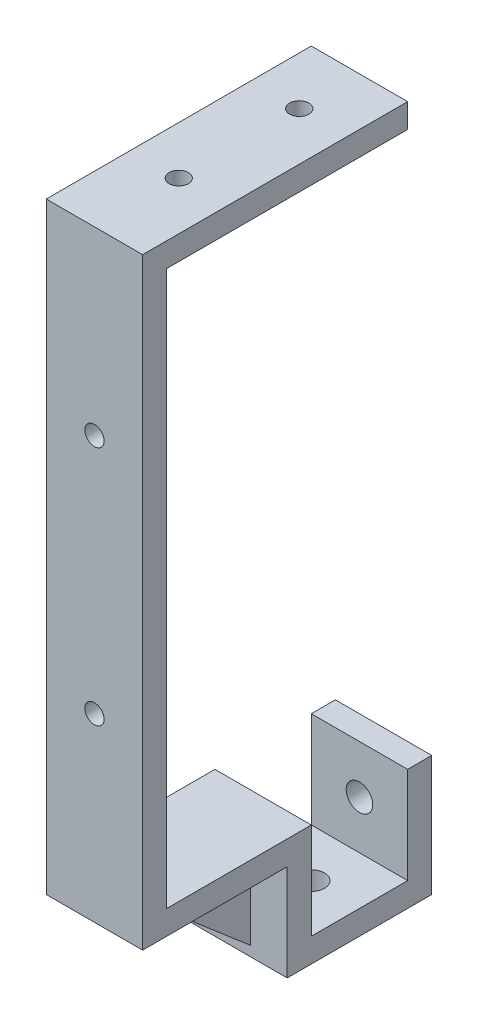
SolidWorks part; units mm, degrees
ref_plane "前视基准面" through (0, 0, 0) normal (0, 0, 1) x (1, 0, 0)
ref_plane "上视基准面" through (0, 0, 0) normal (0, 1, 0) x (1, 0, 0)
ref_plane "右视基准面" through (0, 0, 0) normal (1, 0, 0) x (0, 0, -1)
sketch "草图1" plane through (0, 0, 0) normal (0, 0, 1) x (1, 0, 0)
  line L1 (-9.8291, 14.8718) -> (10.1709, 14.8718)
  line L2 (-9.8291, 14.8718) -> (-9.8291, -130.1282)
  line L3 (-9.8291, -130.1282) -> (10.1709, -130.1282)
  line L4 (10.1709, 14.8718) -> (10.1709, -130.1282)
  dimension "D1" = 20
  dimension "D2" = 145
extrude "凸台-拉伸1" add sketch "草图1" against normal blind 5
sketch "草图2" plane through (0, 0, -5) normal (0, 0, -1) x (-1, 0, 0)
sketch "草图3" plane through (0, 0, -5) normal (0, 0, -1) x (-1, 0, 0)
  line L0 (-10.1709, 9.8718) -> (9.8291, 9.8718)
  line L1 (-10.1709, -130.1282) -> (-10.1709, 14.8718) construction
  line L2 (9.8291, 14.8718) -> (9.8291, -130.1282) construction
  line L3 (-10.1709, 14.8718) -> (9.8291, 14.8718) construction
  line L4 (-10.1709, 9.8718) -> (-10.1709, 14.8718)
  line L5 (-10.1709, 14.8718) -> (9.8291, 14.8718)
  line L6 (9.8291, 14.8718) -> (9.8291, 9.8718)
  dimension "D1" = 5
extrude "凸台-拉伸2" add sketch "草图3" along normal blind 50
sketch "草图4" plane through (0, 0, -5) normal (0, 0, -1) x (-1, 0, 0)
  line L0 (-10.1709, -105.1282) -> (9.8291, -105.1282)
  line L1 (-10.1709, -130.1282) -> (-10.1709, 9.8718) construction
  line L2 (9.8291, 9.8718) -> (9.8291, -130.1282) construction
  line L3 (-10.1709, 9.8718) -> (9.8291, 9.8718) construction
  line L4 (-10.1709, -110.1282) -> (9.8291, -110.1282)
  line L5 (-10.1709, -105.1282) -> (-10.1709, -110.1282)
  line L6 (9.8291, -110.1282) -> (9.8291, -105.1282)
  dimension "D1" = 115
  dimension "D2" = 5
extrude "凸台-拉伸3" add sketch "草图4" along normal blind 30
sketch "草图5" plane through (0, 0, -5) normal (0, 0, -1) x (-1, 0, 0)
  line L4 (9.8291, -110.1282) -> (-10.1709, -110.1282)
  line L5 (-10.1709, -110.1282) -> (-10.1709, -130.1282)
  line L6 (-10.1709, -130.1282) -> (9.8291, -130.1282)
  line L7 (9.8291, -130.1282) -> (9.8291, -110.1282)
  line L8 (9.8291, -110.1282) -> (-10.1709, -110.1282)
  line L9 (-10.1709, -110.1282) -> (-10.1709, -130.1282)
  line L10 (-10.1709, -130.1282) -> (9.8291, -130.1282)
  line L11 (9.8291, -130.1282) -> (9.8291, -110.1282)
  dimension "D1" = 0
extrude "切除-拉伸1" cut sketch "草图5" against normal blind 30
sketch "草图6" plane through (0, -110.1282, 0) normal (0, -1, 0) x (-1, 0, 0)
  line L0 (-10.1709, 30) -> (9.8291, 30)
  line L1 (-10.1709, 35) -> (-10.1709, 0) construction
  line L2 (9.8291, 35) -> (9.8291, 0) construction
  line L3 (-10.1709, 35) -> (9.8291, 35) construction
  line L4 (-10.1709, 30) -> (-10.1709, 35)
  line L5 (-10.1709, 35) -> (9.8291, 35)
  line L6 (9.8291, 35) -> (9.8291, 30)
  dimension "D1" = 5
extrude "凸台-拉伸4" add sketch "草图6" along normal blind 20
sketch "草图7" plane through (0, 0, -35) normal (0, 0, -1) x (-1, 0, 0)
  line L0 (9.8291, -125.1282) -> (-10.1709, -125.1282)
  line L1 (9.8291, -130.1282) -> (9.8291, -105.1282) construction
  line L2 (-10.1709, -105.1282) -> (-10.1709, -130.1282) construction
  line L3 (9.8291, -130.1282) -> (-10.1709, -130.1282) construction
  line L4 (9.8291, -125.1282) -> (9.8291, -130.1282)
  line L5 (9.8291, -130.1282) -> (-10.1709, -130.1282)
  line L6 (-10.1709, -130.1282) -> (-10.1709, -125.1282)
  dimension "D1" = 5
extrude "凸台-拉伸5" add sketch "草图7" along normal blind 20
ref_plane "基准面4" through (0.1709, 0, 0) normal (1, 0, 0) x (0, 0, -1)
sketch "草图9" plane through (0.1709, 0, 0) normal (1, 0, 0) x (0, 0, -1)
  line L0 (8.9653, -110.037) -> (29.9292, -127.9912)
  line L1 (29.9292, -127.9912) -> (29.9292, -110.037)
  line L2 (29.9292, -110.037) -> (8.9653, -110.037)
extrude "凸台-拉伸6" add sketch "草图9" along normal mid plane 5
sketch "草图10" plane through (0, 9.8718, 0) normal (0, -1, 0) x (1, 0, 0)
  circle A0 centre (0.1709, -17.5) radius 2
  circle A1 centre (0.1709, -42.5) radius 2
  dimension "D2" = 4
  dimension "D4" = 4
extrude "切除-拉伸2" cut sketch "草图10" against normal blind 5
sketch "草图11" plane through (0, 0, -5) normal (0, 0, -1) x (-1, 0, 0)
  circle A0 centre (-0.1709, -22.6282) radius 2
  circle A1 centre (-0.1709, -72.6282) radius 2
  dimension "D3" = 4
  dimension "D4" = 4
extrude "切除-拉伸3" cut sketch "草图11" against normal blind 5
sketch "草图12" plane through (0, -125.1282, 0) normal (0, 1, 0) x (1, 0, 0)
  circle A0 centre (0.1709, 45) radius 2.75
  dimension "D1" = 5.5
extrude "切除-拉伸4" cut sketch "草图12" against normal blind 5
sketch "草图13" plane through (0, 0, -55) normal (0, 0, -1) x (-1, 0, 0)
  line L4 (9.8291, -130.1282) -> (9.8291, -125.1282)
  line L5 (9.8291, -125.1282) -> (-10.1709, -125.1282)
  line L6 (-10.1709, -125.1282) -> (-10.1709, -130.1282)
  line L7 (-10.1709, -130.1282) -> (9.8291, -130.1282)
  line L8 (9.8291, -130.1282) -> (9.8291, -125.1282)
  line L9 (9.8291, -125.1282) -> (-10.1709, -125.1282)
  line L10 (-10.1709, -125.1282) -> (-10.1709, -130.1282)
  line L11 (-10.1709, -130.1282) -> (9.8291, -130.1282)
  dimension "D1" = 0
extrude "凸台-拉伸7" add sketch "草图13" along normal blind 5
sketch "草图14" plane through (0, -125.1282, 0) normal (0, 1, 0) x (1, 0, 0)
  line L0 (10.1709, 55) -> (-9.8291, 55)
  line L1 (10.1709, 60) -> (10.1709, 35) construction
  line L2 (-9.8291, 60) -> (-9.8291, 35) construction
  line L3 (-9.8291, 60) -> (10.1709, 60) construction
  line L4 (10.1709, 55) -> (10.1709, 60)
  line L5 (10.1709, 60) -> (-9.8291, 60)
  line L6 (-9.8291, 60) -> (-9.8291, 55)
  dimension "D1" = 5
extrude "凸台-拉伸8" add sketch "草图14" along normal blind 20
sketch "草图15" plane through (0, 0, -55) normal (0, 0, 1) x (1, 0, 0)
  circle A0 centre (0.1709, -115.1282) radius 2.75
  point P0 (0, 0)
  dimension "D1" = 5.5
extrude "切除-拉伸5" cut sketch "草图15" against normal blind 20
